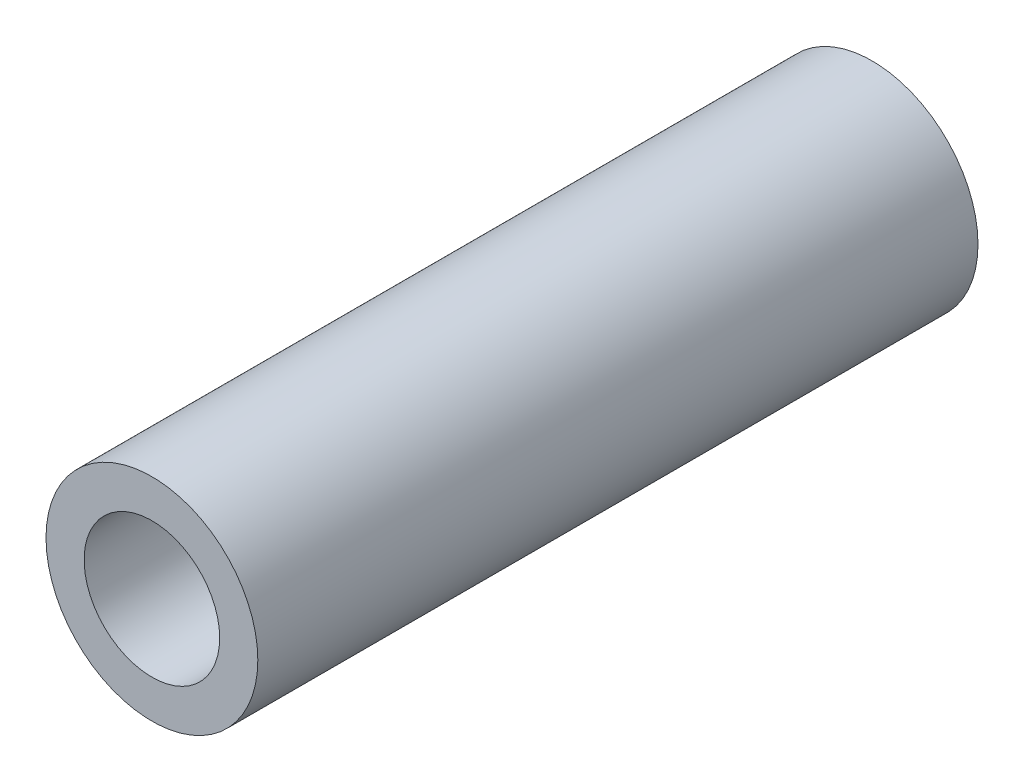
SolidWorks part; units mm, degrees
ref_plane "Front" through (0, 0, 0) normal (0, 0, 1) x (1, 0, 0)
ref_plane "Top" through (0, 0, 0) normal (0, 1, 0) x (1, 0, 0)
ref_plane "Right" through (0, 0, 0) normal (1, 0, 0) x (0, 0, -1)
sketch "Sketch1" plane through (0, 0, 0) normal (0, 0, 1) x (1, 0, 0)
  circle A0 centre (0, 0) radius 2.5
  circle A1 centre (0, 0) radius 1.6
extrude "Boss-Extrude1" add sketch "Sketch1" along normal blind 17
